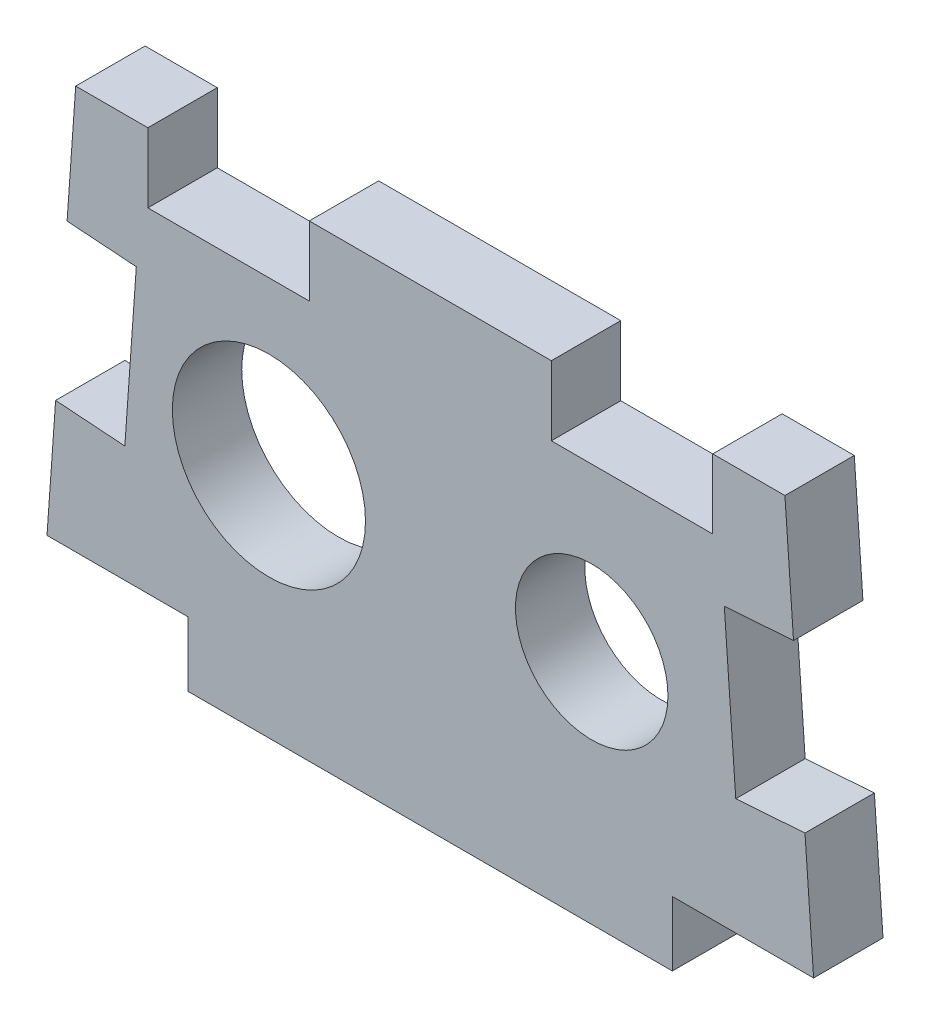
SolidWorks part; units mm, degrees
ref_plane "Front Plane" through (0, 0, 0) normal (0, 0, 1) x (1, 0, 0)
ref_plane "Top Plane" through (0, 0, 0) normal (0, 1, 0) x (1, 0, 0)
ref_plane "Right Plane" through (0, 0, 0) normal (1, 0, 0) x (0, 0, -1)
sketch "Sketch1" plane through (0, 0, 0) normal (0, 0, 1) x (1, 0, 0)
  line L0 (-12.7, -3.0002) -> (12.7, -3.0002) construction
  line L1 (-27.9037, 15.2575) -> (27.9037, 15.2575)
  line L2 (-27.9037, 15.2575) -> (-30.1625, -16.4925)
  line L3 (-30.1625, -16.4925) -> (30.1625, -16.4925)
  line L4 (27.9037, 15.2575) -> (30.1625, -16.4925)
  line L5 (-27.9037, 15.2575) -> (30.1625, -16.4925) construction
  line L6 (-30.1625, -16.4925) -> (27.9037, 15.2575) construction
  line L8 (-24.123, -8.5545) -> (-13.6014, -15.6699) construction
  line L9 (-13.6014, -15.6699) -> (-2.1784, -10.1157) construction
  line L10 (-2.1784, -10.1157) -> (-1.277, 2.554) construction
  line L11 (-1.277, 2.554) -> (-11.7986, 9.6695) construction
  line L12 (-11.7986, 9.6695) -> (-23.2216, 4.1152) construction
  line L13 (-23.2216, 4.1152) -> (-24.123, -8.5545) construction
  circle A0 centre (12.7, -3.0002) radius 6
  circle A1 centre (-12.7, -3.0002) radius 7.6
  circle A2 centre (-12.7, -3.0002) radius 11 construction
  point P0 (0, 0)
  point P8 (0, -3.0002)
  dimension "D1" = 12
  dimension "D2" = 15.2
  dimension "D3" = 5.588
  dimension "D4" = 31.75
  dimension "D5" = 5.461
  dimension "D6" = 60.325
  dimension "D7" = 25.4
  dimension "D8" = 22
extrude "Boss-Extrude1" add sketch "Sketch1" along normal blind 5.461
sketch "Sketch2" plane through (0, 0, 5.461) normal (0, 0, 1) x (1, 0, 0)
  line L0 (27.9037, 15.2575) -> (-27.9037, 15.2575) construction
  line L1 (-22.225, 15.2575) -> (-9.525, 15.2575)
  line L2 (-22.225, 15.2575) -> (-22.225, 9.7965)
  line L3 (-22.225, 9.7965) -> (-9.525, 9.7965)
  line L4 (-9.525, 15.2575) -> (-9.525, 9.7965)
  line L5 (-9.525, 15.2575) -> (9.525, 15.2575) construction
  line L6 (22.225, 15.2575) -> (9.525, 15.2575)
  line L7 (22.225, 15.2575) -> (22.225, 9.7965)
  line L8 (22.225, 9.7965) -> (9.525, 9.7965)
  line L9 (9.525, 15.2575) -> (9.525, 9.7965)
  line L10 (-29.4837, -6.9515) -> (-28.5825, 5.7164)
  line L11 (-29.4837, -6.9515) -> (-24.0365, -7.3391)
  line L12 (-28.5825, 5.7164) -> (-23.1352, 5.3289)
  line L13 (-24.0365, -7.3391) -> (-23.1352, 5.3289)
  line L14 (-27.9037, 15.2575) -> (-30.1625, -16.4925) construction
  line L15 (28.5825, 5.7164) -> (29.4837, -6.9515)
  line L16 (28.5825, 5.7164) -> (23.1352, 5.3289)
  line L17 (29.4837, -6.9515) -> (24.0365, -7.3391)
  line L18 (23.1352, 5.3289) -> (24.0365, -7.3391)
  line L19 (30.1625, -16.4925) -> (27.9037, 15.2575) construction
  point P10 (0, 15.2575)
  point P25 (29.0331, -0.6175)
  point P26 (-29.0331, -0.6175)
  dimension "D1" = 12.7
  dimension "D2" = 19.05
  dimension "D3" = 5.461
extrude "Cut-Extrude1" cut sketch "Sketch2" against normal through all
sketch "Sketch3" plane through (0, 0, 5.461) normal (0, 0, 1) x (1, 0, 0)
  line L0 (-30.1625, -16.4925) -> (30.1625, -16.4925) construction
  line L1 (-19.05, -16.4925) -> (19.05, -16.4925)
  line L2 (-19.05, -16.4925) -> (-19.05, -21.5725)
  line L3 (-19.05, -21.5725) -> (19.05, -21.5725)
  line L4 (19.05, -16.4925) -> (19.05, -21.5725)
  point P6 (0, -16.4925)
  dimension "D1" = 38.1
  dimension "D2" = 5.08
extrude "Boss-Extrude2" add sketch "Sketch3" against normal up to surface (5.461 mm away) up to face at (0, 4.5627, 0)
